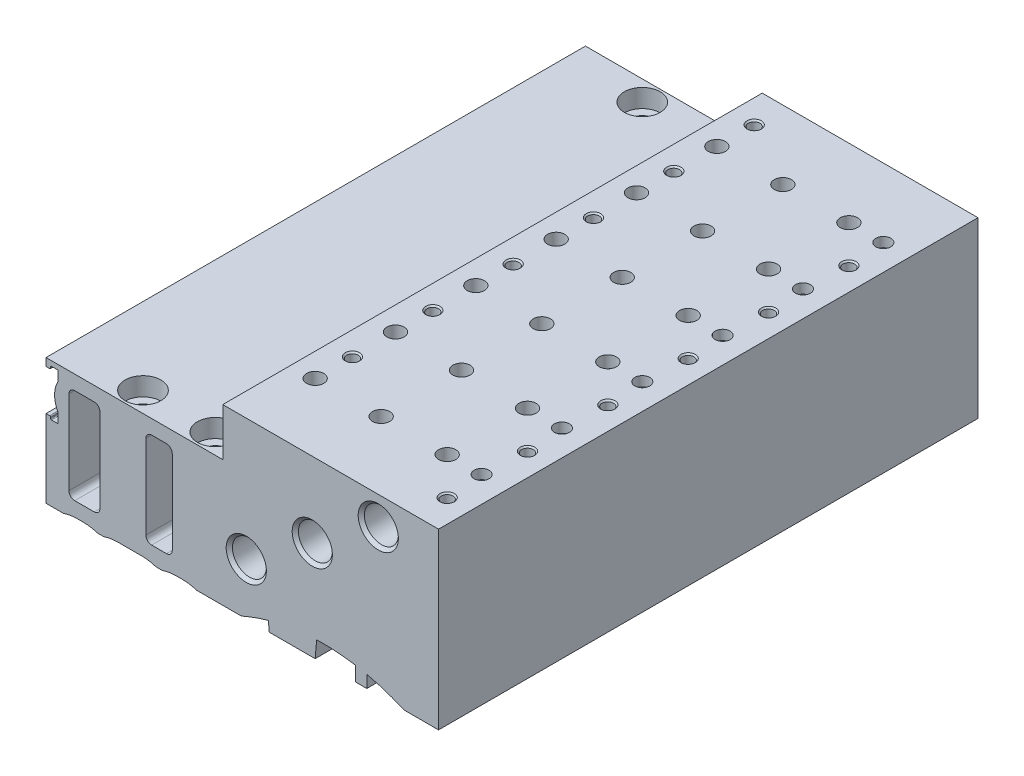
SolidWorks part; units mm, degrees
ref_plane "Front Plane" through (0, 0, 0) normal (0, 0, 1) x (1, 0, 0)
ref_plane "Top Plane" through (0, 0, 0) normal (0, 1, 0) x (1, 0, 0)
ref_plane "Right Plane" through (0, 0, 0) normal (1, 0, 0) x (0, 0, -1)
sketch "Sketch1" plane through (0, 0, 0) normal (0, 0, 1) x (1, 0, 0)
  line L0 (-68.4, 20.65) -> (-67.75, 20.65)
  line L1 (-67.6, 20.8) -> (-67.6, 21)
  line L2 (-67.45, 21.15) -> (-66.45, 21.15)
  line L3 (-66.3, 21) -> (-66.3, 19.4238)
  line L4 (-66.3, 14.7762) -> (-66.3, 13.2)
  line L5 (-66.45, 13.05) -> (-67.45, 13.05)
  line L6 (-67.6, 13.2) -> (-67.6, 13.4)
  line L7 (-67.75, 13.55) -> (-68.4, 13.55)
  line L8 (-68.4, 13.55) -> (-68.4, 0)
  line L9 (-68.4, 0) -> (-65.3995, 0)
  line L10 (-62.95, 0.4) -> (-61.9, 0.4)
  line L11 (-59.4505, 0) -> (-58.3495, 0)
  line L12 (-55.9, 0.4) -> (-51.7, 0.4)
  line L13 (-49.2505, 0) -> (-48.1495, 0)
  line L14 (-45.7, 0.4) -> (-44.6, 0.4)
  line L15 (-42.1505, 0) -> (-34.3774, 0)
  line L16 (-29.6488, 1.7005) -> (-29.5, 0)
  line L17 (-29.5, 0) -> (-21.5, 0)
  line L18 (-21.5, 0) -> (-21.2389, 2.9846)
  line L19 (-14.5, 2.5327) -> (-14.5, 0)
  line L20 (-14.5, 0) -> (-12.5, 0)
  line L21 (-12.5, 0) -> (-12.5, 2.1425)
  line L22 (-6.0226, 0) -> (0, 0)
  line L23 (0, 0) -> (0, 30.3)
  line L24 (0, 30.3) -> (-37.6, 30.3)
  line L25 (-37.6, 30.3) -> (-37.6, 22)
  line L26 (-37.6, 22) -> (-68.4, 22)
  line L27 (-68.4, 22) -> (-68.4, 20.65)
  line L28 (-51, 18.5) -> (-51, 3.9)
  line L29 (-50, 2.9) -> (-47.4, 2.9)
  line L30 (-46.4, 3.9) -> (-46.4, 18.5)
  line L31 (-47.4, 19.5) -> (-50, 19.5)
  line L32 (-64.4, 18.5) -> (-64.4, 3.9)
  line L33 (-63.4, 2.9) -> (-60, 2.9)
  line L34 (-59, 3.9) -> (-59, 18.5)
  line L35 (-60, 19.5) -> (-63.4, 19.5)
  arc A0 (-67.75, 20.65) -> (-67.6, 20.8) centre (-67.75, 20.8) ccw
  arc A1 (-67.6, 21) -> (-67.45, 21.15) centre (-67.45, 21) cw
  arc A2 (-66.45, 21.15) -> (-66.3, 21) centre (-66.45, 21) cw
  arc A3 (-66.3, 19.4238) -> (-66.3, 14.7762) centre (-62.1, 17.1) ccw
  arc A4 (-66.3, 13.2) -> (-66.45, 13.05) centre (-66.45, 13.2) cw
  arc A5 (-67.45, 13.05) -> (-67.6, 13.2) centre (-67.45, 13.2) cw
  arc A6 (-67.6, 13.4) -> (-67.75, 13.55) centre (-67.75, 13.4) ccw
  arc A7 (-65.3995, 0) -> (-62.95, 0.4) centre (-62.95, -7.3) cw
  arc A8 (-61.9, 0.4) -> (-59.4505, 0) centre (-61.9, -7.3) cw
  arc A9 (-58.3495, 0) -> (-55.9, 0.4) centre (-55.9, -7.3) cw
  arc A10 (-51.7, 0.4) -> (-49.2505, 0) centre (-51.7, -7.3) cw
  arc A11 (-48.1495, 0) -> (-45.7, 0.4) centre (-45.7, -7.3) cw
  arc A12 (-44.6, 0.4) -> (-42.1505, 0) centre (-44.6, -7.3) cw
  arc A13 (-34.3774, 0) -> (-29.6488, 1.7005) centre (-20.2, -32) cw
  arc A14 (-21.2389, 2.9846) -> (-14.5, 2.5327) centre (-20.2, -32) cw
  arc A15 (-12.5, 2.1425) -> (-6.0226, 0) centre (-20.2, -32) cw
  arc A16 (-51, 3.9) -> (-50, 2.9) centre (-50, 3.9) ccw
  arc A17 (-47.4, 2.9) -> (-46.4, 3.9) centre (-47.4, 3.9) ccw
  arc A18 (-46.4, 18.5) -> (-47.4, 19.5) centre (-47.4, 18.5) ccw
  arc A19 (-50, 19.5) -> (-51, 18.5) centre (-50, 18.5) ccw
  arc A20 (-64.4, 3.9) -> (-63.4, 2.9) centre (-63.4, 3.9) ccw
  arc A21 (-60, 2.9) -> (-59, 3.9) centre (-60, 3.9) ccw
  arc A22 (-59, 18.5) -> (-60, 19.5) centre (-60, 18.5) ccw
  arc A23 (-63.4, 19.5) -> (-64.4, 18.5) centre (-63.4, 18.5) ccw
extrude "Boss-Extrude1" add sketch "Sketch1" along normal blind 94
ref_plane "Plane1" through (0, 0, 6.5) normal (0, 0, 1) x (1, 0, 0)
hole_wizard "Hole1" positions "Sketch3" profile "Sketch2" legacy
sketch "Sketch3" plane through (0, 0, 0) normal (0, -1, 0) x (-1, 0, 0)
  point P0 (25.5, -6.5)
sketch "Sketch2" plane through (-25.5, 0, 6.5) normal (1, 0, 0) x (0, 0, -1)
  line L0 (0, 0) -> (0, 10.0681)
  line L1 (0, 10.0681) -> (1.85, 9)
  line L2 (1.85, 9) -> (1.85, 0)
  line L4 (1.85, 0) -> (0, 0)
  line L6 (0, 10.0681) -> (-1.85, 9) construction
  line L7 (0, -4.2442) -> (0, 117.3081) construction
  dimension "Diameter" = 3.7
  dimension "Depth" = 9
  dimension "Drill Angle" = 120
ref_plane "Plane2" through (0, 0, 87.5) normal (0, 0, 1) x (1, 0, 0)
hole_wizard "Hole2" positions "Sketch5" profile "Sketch4" legacy
sketch "Sketch5" plane through (0, 0, 0) normal (0, -1, 0) x (-1, 0, 0)
  point P0 (25.5, -87.5)
sketch "Sketch4" plane through (-25.5, 0, 87.5) normal (1, 0, 0) x (0, 0, -1)
  line L0 (0, 0) -> (0, 10.0681)
  line L1 (0, 10.0681) -> (1.85, 9)
  line L2 (1.85, 9) -> (1.85, 0)
  line L4 (1.85, 0) -> (0, 0)
  line L6 (0, 10.0681) -> (-1.85, 9) construction
  line L7 (0, -4.2442) -> (0, 117.3081) construction
  dimension "Diameter" = 3.7
  dimension "Depth" = 9
  dimension "Drill Angle" = 120
ref_plane "Plane3" through (-33.5, 0, 0) normal (1, 0, 0) x (0, 0, -1)
sketch "Sketch6" plane through (-33.5, 0, 0) normal (1, 0, 0) x (0, 0, -1)
  line L0 (-94, 9) -> (-94, 12.5)
  line L1 (-94, 12.5) -> (-93.4585, 11.9585)
  line L2 (-93.4585, 11.9585) -> (-0.5415, 11.9585)
  line L3 (-0.5415, 11.9585) -> (0, 12.5)
  line L4 (0, 12.5) -> (0, 9)
  line L5 (0, 9) -> (-94, 9)
  line L6 (0, 9) -> (-94, 9) construction
revolve "Cut-Revolve1" cut sketch "Sketch6" angle 360 about L6
cosmetic thread "Cosmetic Thread1" parameters "D1"=9, "D2"=7
cosmetic thread "Cosmetic Thread2" parameters "D1"=9, "D2"=7
ref_plane "Plane4" through (-22, 0, 0) normal (1, 0, 0) x (0, 0, -1)
sketch "Sketch7" plane through (-22, 0, 0) normal (1, 0, 0) x (0, 0, -1)
  line L0 (-94, 17.2) -> (-94, 20.7)
  line L1 (-94, 20.7) -> (-93.4585, 20.1585)
  line L2 (-93.4585, 20.1585) -> (-0.5415, 20.1585)
  line L3 (-0.5415, 20.1585) -> (0, 20.7)
  line L4 (0, 20.7) -> (0, 17.2)
  line L5 (0, 17.2) -> (-94, 17.2)
  line L6 (0, 17.2) -> (-94, 17.2) construction
revolve "Cut-Revolve2" cut sketch "Sketch7" angle 360 about L6
cosmetic thread "Cosmetic Thread3" parameters "D1"=9, "D2"=7
cosmetic thread "Cosmetic Thread4" parameters "D1"=9, "D2"=7
ref_plane "Plane5" through (-10.5, 0, 0) normal (1, 0, 0) x (0, 0, -1)
sketch "Sketch8" plane through (-10.5, 0, 0) normal (1, 0, 0) x (0, 0, -1)
  line L0 (-94, 25.4) -> (-94, 28.9)
  line L1 (-94, 28.9) -> (-93.4585, 28.3585)
  line L2 (-93.4585, 28.3585) -> (-0.5415, 28.3585)
  line L3 (-0.5415, 28.3585) -> (0, 28.9)
  line L4 (0, 28.9) -> (0, 25.4)
  line L5 (0, 25.4) -> (-94, 25.4)
  line L6 (0, 25.4) -> (-94, 25.4) construction
revolve "Cut-Revolve3" cut sketch "Sketch8" angle 360 about L6
cosmetic thread "Cosmetic Thread5" parameters "D1"=9, "D2"=7
cosmetic thread "Cosmetic Thread6" parameters "D1"=9, "D2"=7
ref_plane "Plane6" through (0, 0, 3.5) normal (0, 0, 1) x (1, 0, 0)
sketch "Sketch9" plane through (0, 0, 3.5) normal (0, 0, 1) x (1, 0, 0)
  line L0 (-55, 22) -> (-51.875, 22)
  line L1 (-51.875, 22) -> (-51.875, 18.8)
  line L2 (-51.875, 18.8) -> (-53.35, 18.8)
  line L3 (-53.35, 18.8) -> (-53.35, 0)
  line L4 (-53.35, 0) -> (-55, 0)
  line L5 (-55, 0) -> (-55, 22)
  line L6 (-55, 0) -> (-55, 22) construction
revolve "Cut-Revolve4" cut sketch "Sketch9" angle 360 about L6
sketch "Sketch10" plane through (0, 0, 3.5) normal (0, 0, 1) x (1, 0, 0)
  line L0 (-42.4, 22) -> (-39.275, 22)
  line L1 (-39.275, 22) -> (-39.275, 18.8)
  line L2 (-39.275, 18.8) -> (-40.75, 18.8)
  line L3 (-40.75, 18.8) -> (-40.75, 0)
  line L4 (-40.75, 0) -> (-42.4, 0)
  line L5 (-42.4, 0) -> (-42.4, 22)
  line L6 (-42.4, 0) -> (-42.4, 22) construction
revolve "Cut-Revolve5" cut sketch "Sketch10" angle 360 about L6
ref_plane "Plane7" through (0, 0, 90.5) normal (0, 0, 1) x (1, 0, 0)
sketch "Sketch11" plane through (0, 0, 90.5) normal (0, 0, 1) x (1, 0, 0)
  line L0 (-55, 22) -> (-51.875, 22)
  line L1 (-51.875, 22) -> (-51.875, 18.8)
  line L2 (-51.875, 18.8) -> (-53.35, 18.8)
  line L3 (-53.35, 18.8) -> (-53.35, 0)
  line L4 (-53.35, 0) -> (-55, 0)
  line L5 (-55, 0) -> (-55, 22)
  line L6 (-55, 0) -> (-55, 22) construction
revolve "Cut-Revolve6" cut sketch "Sketch11" angle 360 about L6
sketch "Sketch12" plane through (0, 0, 90.5) normal (0, 0, 1) x (1, 0, 0)
  line L0 (-42.4, 22) -> (-39.275, 22)
  line L1 (-39.275, 22) -> (-39.275, 18.8)
  line L2 (-39.275, 18.8) -> (-40.75, 18.8)
  line L3 (-40.75, 18.8) -> (-40.75, 0)
  line L4 (-40.75, 0) -> (-42.4, 0)
  line L5 (-42.4, 0) -> (-42.4, 22)
  line L6 (-42.4, 0) -> (-42.4, 22) construction
revolve "Cut-Revolve7" cut sketch "Sketch12" angle 360 about L6
ref_plane "Plane8" through (0, 30.3, 0) normal (0, 1, 0) x (1, 0, 0)
sketch "Sketch13" plane through (0, 30.3, 0) normal (0, 1, 0) x (1, 0, 0)
  circle A0 centre (-10.5, -82) radius 1.5
extrude "Cut-Extrude1" cut sketch "Sketch13" against normal blind 7
sketch "Sketch14" plane through (0, 30.3, 0) normal (0, 1, 0) x (1, 0, 0)
  line L0 (-10.5, -82) -> (-10.5, -12)
pattern_linear "LPattern1" count 6 spacing 14 along (0, 0, -1) of "Cut-Extrude1"
sketch "Sketch15" plane through (0, 30.3, 0) normal (0, 1, 0) x (1, 0, 0)
  circle A0 centre (-22, -82) radius 1.5
extrude "Cut-Extrude2" cut sketch "Sketch15" against normal blind 12
sketch "Sketch16" plane through (0, 30.3, 0) normal (0, 1, 0) x (1, 0, 0)
  line L0 (-22, -82) -> (-22, -12)
pattern_linear "LPattern2" count 6 spacing 14 along (0, 0, -1) of "Cut-Extrude2"
sketch "Sketch17" plane through (0, 30.3, 0) normal (0, 1, 0) x (1, 0, 0)
  circle A0 centre (-33.5, -82) radius 1.5
extrude "Cut-Extrude3" cut sketch "Sketch17" against normal blind 22
sketch "Sketch18" plane through (0, 30.3, 0) normal (0, 1, 0) x (1, 0, 0)
  line L0 (-33.5, -82) -> (-33.5, -12)
pattern_linear "LPattern3" count 6 spacing 14 along (0, 0, -1) of "Cut-Extrude3"
sketch "Sketch19" plane through (0, 30.3, 0) normal (0, 1, 0) x (1, 0, 0)
  circle A0 centre (-4.5, -82) radius 1.3
extrude "Cut-Extrude4" cut sketch "Sketch19" against normal blind 1.7
sketch "Sketch20" plane through (0, 30.3, 0) normal (0, 1, 0) x (1, 0, 0)
  line L0 (-4.5, -82) -> (-4.5, -12)
pattern_linear "LPattern4" count 6 spacing 14 along (0, 0, -1) of "Cut-Extrude4"
ref_plane "Plane9" through (-33.5, 0, 0) normal (1, 0, 0) x (0, 0, -1)
sketch "Sketch21" plane through (-33.5, 0, 0) normal (1, 0, 0) x (0, 0, -1)
  line L0 (-75.5, 30.3) -> (-74.25, 30.3)
  line L1 (-74.25, 30.3) -> (-74.4935, 30.0565)
  line L2 (-74.4935, 30.0565) -> (-74.4935, 25.7)
  line L3 (-74.4935, 25.7) -> (-75.5, 25.7)
  line L4 (-75.5, 25.7) -> (-75.5, 30.3)
  line L5 (-75.5, 25.7) -> (-75.5, 30.3) construction
revolve "Cut-Revolve8" cut sketch "Sketch21" angle 360 about L5
cosmetic thread "Cosmetic Thread7" parameters "D1"=4.3, "D2"=2.5
sketch "Sketch22" plane through (-33.5, 0, 0) normal (1, 0, 0) x (0, 0, -1)
  line L0 (-75.5, 30.3) -> (-5.5, 30.3)
pattern_linear "LPattern5" count 6 spacing 14 along (0, 0, -1) of "Cut-Revolve8"
ref_plane "Plane10" through (-4, 0, 0) normal (1, 0, 0) x (0, 0, -1)
sketch "Sketch23" plane through (-4, 0, 0) normal (1, 0, 0) x (0, 0, -1)
  line L0 (-88.5, 30.3) -> (-87.25, 30.3)
  line L1 (-87.25, 30.3) -> (-87.4935, 30.0565)
  line L2 (-87.4935, 30.0565) -> (-87.4935, 25.7)
  line L3 (-87.4935, 25.7) -> (-88.5, 25.7)
  line L4 (-88.5, 25.7) -> (-88.5, 30.3)
  line L5 (-88.5, 25.7) -> (-88.5, 30.3) construction
revolve "Cut-Revolve9" cut sketch "Sketch23" angle 360 about L5
cosmetic thread "Cosmetic Thread8" parameters "D1"=4.3, "D2"=2.5
sketch "Sketch24" plane through (-4, 0, 0) normal (1, 0, 0) x (0, 0, -1)
  line L0 (-88.5, 30.3) -> (-18.5, 30.3)
pattern_linear "LPattern6" count 6 spacing 14 along (0, 0, -1) of "Cut-Revolve9"
